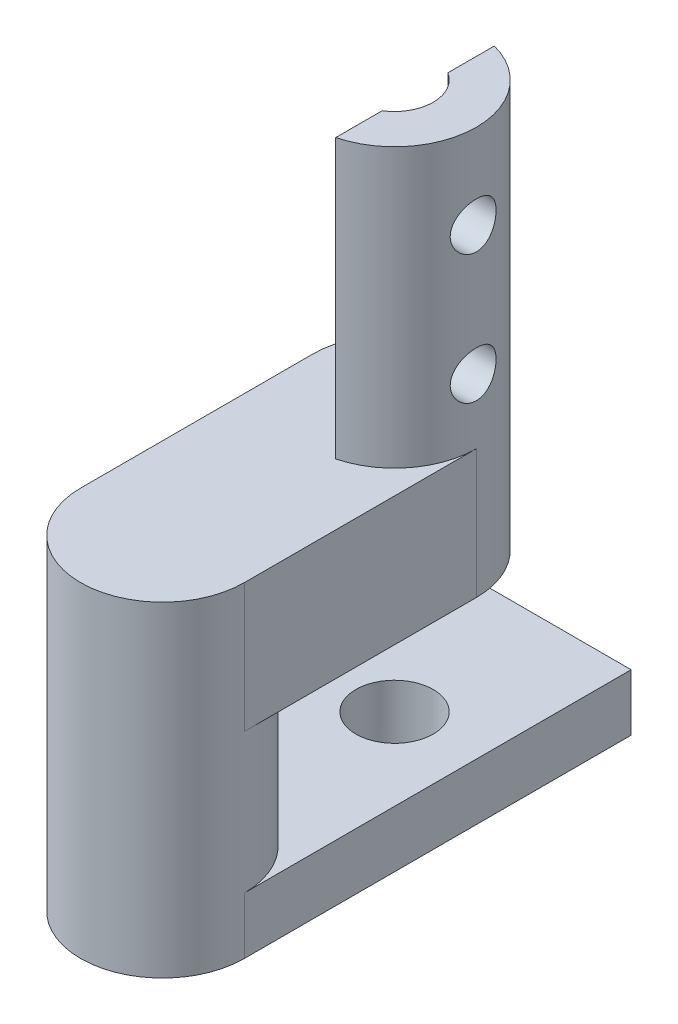
SolidWorks part; units mm, degrees
ref_plane "Front" through (0, 0, 0) normal (0, 0, 1) x (1, 0, 0)
ref_plane "Top" through (0, 0, 0) normal (0, 1, 0) x (1, 0, 0)
ref_plane "Right" through (0, 0, 0) normal (1, 0, 0) x (0, 0, -1)
sketch "草图1" plane through (0, 0, 0) normal (0, 1, 0) x (1, 0, 0)
  circle A0 centre (0, 0) radius 3.175
extrude "凸台-拉伸1" add sketch "草图1" along normal blind 57.15
sketch "草图2" plane through (0, 57.15, 0) normal (0, 1, 0) x (1, 0, 0)
  line L0 (0, 0) -> (0, 3.175) construction
  line L2 (0.794, 3.175) -> (0.794, -3.175)
  line L3 (0.794, -3.175) -> (-3.175, -3.175)
  line L4 (-3.175, -3.175) -> (-3.175, 3.175)
  line L6 (0, 0) -> (0.794, 0) construction
  line L7 (-3.175, 3.175) -> (-3.175, 13.175)
  line L8 (-3.175, 13.175) -> (0.794, 13.175)
  line L9 (0.794, 13.175) -> (0.794, 3.175)
  circle A0 centre (0, 0) radius 3.175 construction
  point P8 (0, 3.175)
extrude "切除-拉伸1" cut sketch "草图2" against normal blind 10.795
sketch "草图3" plane through (0.794, 0, 0) normal (-1, 0, 0) x (0, 0, 1)
  line L0 (0, 57.15) -> (0, 53.855) construction
  line L1 (3.0741, 57.15) -> (-3.0741, 57.15) construction
  line L2 (0, 57.15) -> (0, 48.855) construction
  line L3 (0, 53.855) -> (0, 57.15) construction
  circle A0 centre (0, 53.855) radius 0.889
  circle A1 centre (0, 48.855) radius 0.889
extrude "切除-拉伸2" cut sketch "草图3" against normal blind 10.795
sketch "草图4" plane through (0, 0, 0) normal (0, -1, 0) x (1, 0, 0)
  circle A0 centre (0, 0) radius 3.175
extrude "切除-拉伸3" cut sketch "草图4" against normal blind 34.83
sketch "草图5" plane through (0, 34.83, 0) normal (0, -1, 0) x (1, 0, 0)
  line L0 (0, 0) -> (3.175, 0) construction
  line L1 (3.175, 0) -> (3.175, -15) construction
  line L2 (3.175, -15) -> (-3.175, -15) construction
  line L3 (-3.175, -15) -> (-3.175, 0) construction
  line L4 (0, -15) -> (0, -9) construction
  line L6 (3.175, 0) -> (3.175, -15)
  line L7 (3.175, -15) -> (-3.175, -15)
  line L8 (-3.175, -15) -> (-3.175, 0)
  line L9 (0, -9) -> (0, 0) construction
  circle A0 centre (0, 0) radius 3.175 construction
  circle A1 centre (0, -9) radius 1.5
  arc A2 (3.175, 0) -> (-3.175, 0) centre (0, 0) ccw
extrude "凸台-拉伸2" add sketch "草图5" along normal mid plane 2.2
sketch "草图6" plane through (0, 35.93, 0) normal (0, 1, 0) x (1, 0, 0)
  circle A0 centre (0, 9) radius 3.175
extrude "凸台-拉伸3" add sketch "草图6" along normal blind 21.22
sketch "草图7" plane through (0, 33.73, 0) normal (0, -1, 0) x (1, 0, 0)
  circle A0 centre (0, -9) radius 1.5
extrude "切除-拉伸4" cut sketch "草图7" against normal blind 28
sketch "草图8" plane through (0, 57.15, 0) normal (0, 1, 0) x (1, 0, 0)
  line L0 (0, 9) -> (0, 12.175) construction
  line L1 (0, 12.175) -> (0.794, 12.175) construction
  line L2 (0.794, 12.175) -> (0.794, 5.825) construction
  line L3 (0.794, 5.825) -> (-3.175, 5.825) construction
  line L4 (-3.175, 0) -> (-3.175, 9) construction
  line L5 (-3.175, 5.825) -> (-3.175, 12.175) construction
  line L6 (-3.175, 9) -> (-3.175, 15) construction
  line L7 (-3.175, 12.175) -> (0.794, 12.175) construction
  line L8 (-3.175, 12.175) -> (0.794, 12.175)
  line L9 (0.794, 12.175) -> (0.794, 5.825)
  line L10 (0.794, 5.825) -> (-3.175, 5.825)
  line L11 (-3.175, 5.825) -> (-3.175, 12.175)
  circle A0 centre (0, 9) radius 3.175 construction
extrude "切除-拉伸5" cut sketch "草图8" against normal blind 10.795
sketch "草图9" plane through (0.794, 0, 0) normal (-1, 0, 0) x (0, 0, 1)
  line L0 (-9, 57.15) -> (-9, 53.855) construction
  line L1 (-7.7274, 57.15) -> (-10.2726, 57.15) construction
  line L2 (-9, 53.855) -> (-5.9259, 53.855) construction
  line L3 (-5.9259, 57.15) -> (-5.9259, 46.355) construction
  line L4 (-5.9259, 53.855) -> (-5.9259, 51.7525) construction
  line L5 (-5.9259, 51.7525) -> (-9, 51.7525) construction
  line L6 (-9, 51.7525) -> (-9, 48.855) construction
  circle A0 centre (-9, 48.855) radius 0.889
  circle A1 centre (-9, 53.855) radius 0.889
extrude "切除-拉伸6" cut sketch "草图9" against normal blind 10.795
sketch "草图10" plane through (0, 46.355, 0) normal (0, 1, 0) x (1, 0, 0)
  line L0 (-3.175, 0) -> (-3.175, 9)
  line L1 (3.175, 9) -> (3.175, 0)
  arc A0 (0.794, 3.0741) -> (0.794, -3.0741) centre (0, 0) ccw construction
  arc A1 (0.794, 12.0741) -> (0.794, 5.9259) centre (0, 9) ccw construction
  arc A2 (0.794, 5.9259) -> (0.794, 12.0741) centre (0, 9) ccw construction
  arc A3 (0.794, -3.0741) -> (0.794, 3.0741) centre (0, 0) ccw construction
  arc A4 (3.175, 0) -> (-3.175, 0) centre (0, 0) ccw
  arc A5 (-3.175, 9) -> (3.175, 9) centre (0, 9) ccw
extrude "凸台-拉伸4" add sketch "草图10" against normal blind 5
sketch "草图11" plane through (0, 35.93, 0) normal (0, 1, 0) x (1, 0, 0)
  circle A0 centre (0, 9) radius 3.175
extrude "切除-拉伸7" cut sketch "草图11" along normal blind 5.425
sketch "草图13" plane through (0, 46.355, 0) normal (0, 1, 0) x (1, 0, 0)
  circle A0 centre (0, 0) radius 3.175
extrude "切除-拉伸8" cut sketch "草图13" along normal blind 10.795
